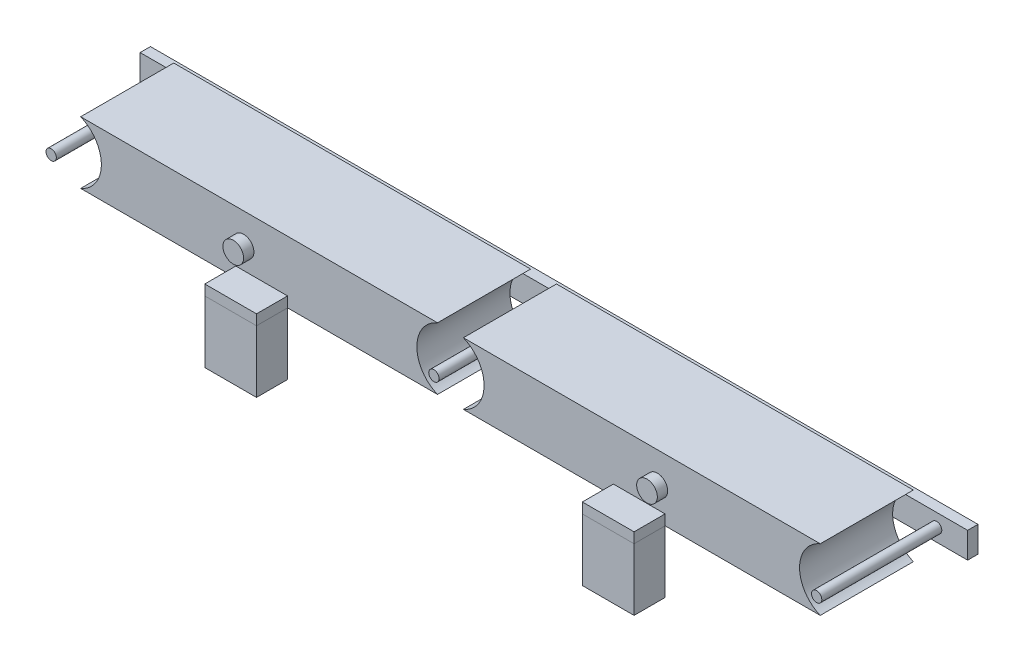
SolidWorks part; units mm, degrees
ref_plane "Front Plane" through (0, 0, 0) normal (0, 0, 1) x (1, 0, 0)
ref_plane "Top Plane" through (0, 0, 0) normal (0, 1, 0) x (1, 0, 0)
ref_plane "Right Plane" through (0, 0, 0) normal (1, 0, 0) x (0, 0, -1)
sketch "Sketch1" plane through (0, 0, 0) normal (0, 1, 0) x (1, 0, 0)
  line L1 (-400, 45) -> (400, 45)
  line L2 (-400, 45) -> (-400, -45)
  line L3 (-400, -45) -> (400, -45)
  line L4 (400, 45) -> (400, -45)
  line L5 (-400, 45) -> (400, -45) construction
  line L6 (-400, -45) -> (400, 45) construction
  point P0 (0, 0)
  dimension "D1" = 90
  dimension "D2" = 800
extrude "Boss-Extrude1" add sketch "Sketch1" along normal blind 60
ref_plane "Plane1" through (0, 0, 45) normal (0, 0, 1) x (1, 0, 0)
sketch "Sketch2" plane through (0, 0, 45) normal (0, 0, 1) x (1, 0, 0)
  line L0 (400, 60) -> (400, 0) construction
  line L1 (-400, 60) -> (400, 60) construction
  circle A0 centre (370, 30) radius 32.5
  circle A1 centre (-370, 30) radius 32.5
  circle A2 centre (0, 30) radius 32.5
  dimension "D1" = 65
  dimension "D2" = 30
  dimension "D3" = 30
  dimension "D4" = 2
  dimension "D5" = 2
extrude "Cut-Extrude1" cut sketch "Sketch2" against normal blind 110
ref_plane "Plane2" through (0, 0, -55) normal (0, 0, -1) x (-1, 0, 0)
sketch "Sketch3" plane through (0, 0, -55) normal (0, 0, -1) x (-1, 0, 0)
  line L5 (-400, 42.5) -> (400, 42.5)
  line L6 (-400, 42.5) -> (-400, 17.5)
  line L7 (-400, 17.5) -> (400, 17.5)
  line L8 (400, 42.5) -> (400, 17.5)
extrude "Boss-Extrude2" add sketch "Sketch3" along normal blind 10 separate body
sketch "Sketch4" plane through (0, 0, -55) normal (0, 0, -1) x (-1, 0, 0)
  line L0 (400, 17.5) -> (400, 42.5) construction
  line L1 (-400, 42.5) -> (-400, 17.5) construction
  circle A0 centre (-200, 30.4133) radius 10
  circle A1 centre (200, 30.4133) radius 10
  dimension "D1" = 20
  dimension "D2" = 20
  dimension "D3" = 200
  dimension "D4" = 200
extrude "Boss-Extrude3" add sketch "Sketch4" against normal blind 20
ref_plane "Plane3" through (0, 0, -65) normal (0, 0, -1) x (-1, 0, 0)
sketch "Sketch5" plane through (0, 0, -65) normal (0, 0, -1) x (-1, 0, 0)
  circle A0 centre (-370, 30) radius 5
  arc A1 (-357.5, 0) -> (-357.5, 60) centre (-370, 30) ccw construction
  circle A2 centre (0, 30) radius 5
  arc A3 (12.5, 0) -> (12.5, 60) centre (0, 30) ccw construction
  circle A4 centre (370, 30) radius 5
  arc A5 (357.5, 60) -> (357.5, 0) centre (370, 30) ccw construction
  dimension "D1" = 10
  dimension "D2" = 0
  dimension "D3" = 10
  dimension "D4" = 0
  dimension "D5" = 10
  dimension "D6" = 0
extrude "Boss-Extrude5" add sketch "Sketch5" against normal blind 126
ref_plane "Plane4" through (0, 10, 0) normal (0, 1, 0) x (1, 0, 0)
sketch "Sketch6" plane through (0, 10, 0) normal (0, 1, 0) x (1, 0, 0)
  line L0 (357.5, 45) -> (357.5, -45) construction
  line L1 (157.5, 75) -> (207.5, 75)
  line L2 (157.5, 75) -> (157.5, -75)
  line L3 (157.5, -75) -> (207.5, -75)
  line L4 (207.5, 75) -> (207.5, -75)
  line L5 (157.5, 75) -> (207.5, -75) construction
  line L6 (157.5, -75) -> (207.5, 75) construction
  line L7 (-207.5, 75) -> (-157.5, 75)
  line L8 (-207.5, 75) -> (-207.5, -75)
  line L9 (-207.5, -75) -> (-157.5, -75)
  line L10 (-157.5, 75) -> (-157.5, -75)
  line L11 (-207.5, 75) -> (-157.5, -75) construction
  line L12 (-207.5, -75) -> (-157.5, 75) construction
  line L13 (-357.5, -45) -> (-357.5, 45) construction
  line L14 (12.5, -45) -> (357.5, -45) construction
  line L16 (-357.5, -45) -> (-12.5, -45) construction
  point P0 (182.5, 0)
  point P5 (-182.5, 0)
  dimension "D1" = 150
  dimension "D2" = 150
  dimension "D3" = 50
  dimension "D4" = 50
  dimension "D5" = 150
  dimension "D6" = 150
  dimension "D7" = 30
  dimension "D8" = 30
extrude "Boss-Extrude6" add sketch "Sketch6" against normal blind 10 separate body
sketch "Sketch8" plane through (0, 0, 0) normal (0, 1, 0) x (1, 0, 0)
  line L0 (-157.5, -75) -> (-157.5, 75) construction
  line L1 (-207.5, -75) -> (-157.5, -75)
  line L2 (-207.5, -75) -> (-207.5, -45)
  line L3 (-207.5, -45) -> (-157.5, -45)
  line L4 (-157.5, -75) -> (-157.5, -45)
  line L5 (-357.5, -45) -> (-12.5, -45) construction
  line L6 (-12.5, 45) -> (-357.5, 45) construction
  line L7 (-207.5, 75) -> (-157.5, 75)
  line L8 (-207.5, 75) -> (-207.5, 45)
  line L9 (-207.5, 45) -> (-157.5, 45)
  line L10 (-157.5, 75) -> (-157.5, 45)
  line L11 (207.5, -75) -> (207.5, 75) construction
  line L12 (157.5, 75) -> (207.5, 75)
  line L13 (157.5, 75) -> (157.5, 45)
  line L14 (157.5, 45) -> (207.5, 45)
  line L15 (207.5, 75) -> (207.5, 45)
  line L16 (357.5, 45) -> (12.5, 45) construction
  line L17 (12.5, -45) -> (357.5, -45) construction
  line L18 (157.5, -75) -> (207.5, -75)
  line L19 (157.5, -75) -> (157.5, -45)
  line L20 (157.5, -45) -> (207.5, -45)
  line L21 (207.5, -75) -> (207.5, -45)
extrude "Boss-Extrude7" add sketch "Sketch8" against normal blind 60 separate body
ref_plane "Plane5" through (0, 0, 45) normal (0, 0, 1) x (1, 0, 0)
sketch "Sketch9" plane through (0, 0, 45) normal (0, 0, 1) x (1, 0, 0)
  circle A0 centre (-200, 30.4133) radius 10
  circle A1 centre (200, 30.4133) radius 10
extrude "Boss-Extrude8" add sketch "Sketch9" along normal blind 10
sketch "Sketch11" plane through (0, 0, 0) normal (0, 1, 0) x (1, 0, 0)
  line L0 (400, 55) -> (-400, 55) construction
  line L1 (414.7169, -53.3854) -> (376.4579, -53.3854)
  line L2 (414.7169, -53.3854) -> (414.7169, 52.1166)
  line L3 (414.7169, 52.1166) -> (376.4579, 52.1166)
  line L4 (376.4579, -53.3854) -> (376.4579, 52.1166)
  line L5 (-413.0042, -53.3854) -> (-378.5043, -53.3854)
  line L6 (-413.0042, -53.3854) -> (-413.0042, 55)
  line L7 (-413.0042, 55) -> (-378.5043, 55)
  line L8 (-378.5043, -53.3854) -> (-378.5043, 55)
extrude "Cut-Extrude3" cut sketch "Sketch11" along normal blind 100
